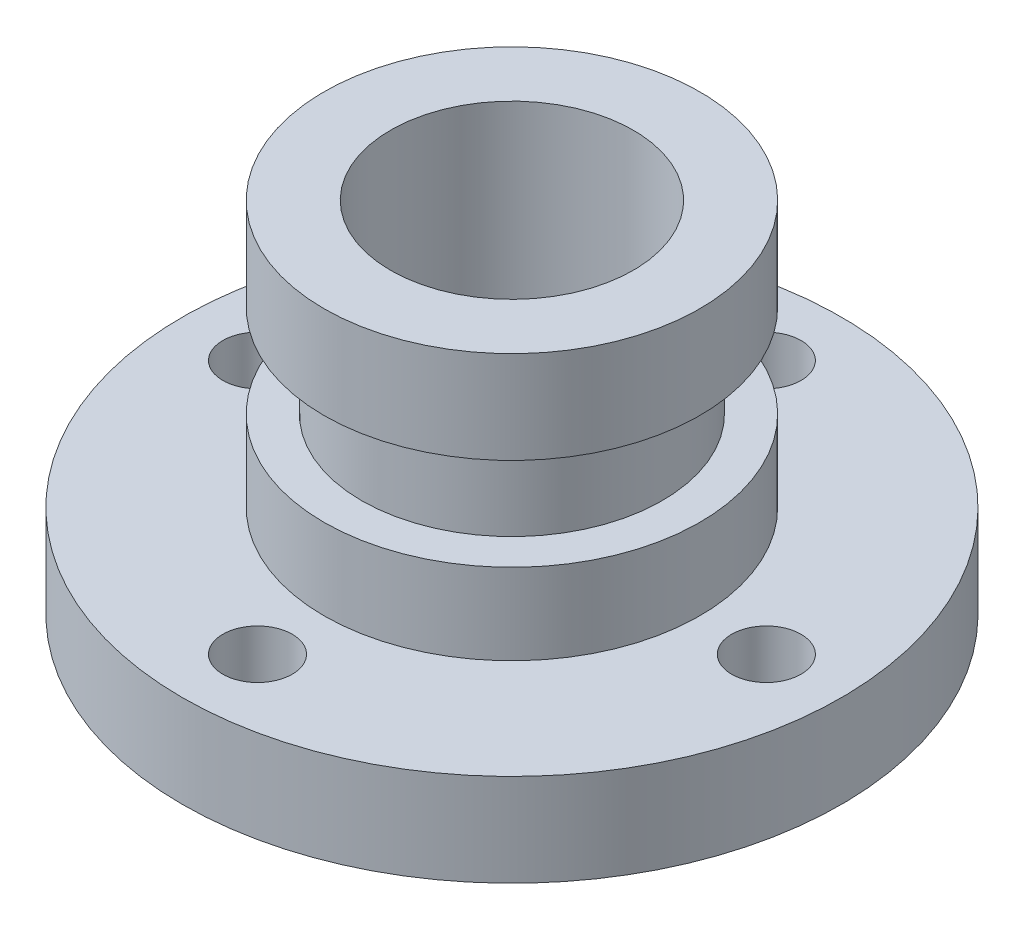
SolidWorks part; units mm, degrees
ref_plane "정면" through (0, 0, 0) normal (0, 0, 1) x (1, 0, 0)
ref_plane "윗면" through (0, 0, 0) normal (0, 1, 0) x (1, 0, 0)
ref_plane "우측면" through (0, 0, 0) normal (1, 0, 0) x (0, 0, -1)
sketch "스케치2" plane through (0, 0, 0) normal (0, 0, 1) x (1, 0, 0)
  line L0 (0, 81.32) -> (0, -101.1226) construction
  line L1 (0, 0) -> (57, 0)
  line L2 (57, 0) -> (57, 16)
  line L3 (57, 16) -> (32.5, 16)
  line L4 (32.5, 16) -> (32.5, 30)
  line L5 (32.5, 30) -> (26, 30)
  line L6 (26, 30) -> (26, 46)
  line L7 (26, 46) -> (32.5, 46)
  line L8 (32.5, 46) -> (32.5, 62)
  line L9 (32.5, 62) -> (0, 62)
  line L10 (0, 62) -> (0, 0)
  point P9 (0, 0)
  point P14 (0, -101.1226)
  point P15 (26, 51.6557)
  dimension "D1" = 57
  dimension "D2" = 32.5
  dimension "D3" = 26
  dimension "D4" = 32.5
  dimension "D5" = 16
  dimension "D6" = 62
  dimension "D7" = 16
  dimension "D8" = 16
revolve "회전1" add sketch "스케치2" angle 360 about L0
sketch "스케치5" plane through (0, 0, 0) normal (0, 0, 1) x (1, 0, 0)
  line L0 (0, 0) -> (15, 0)
  line L1 (-57, 0) -> (57, 0) construction
  line L2 (15, 0) -> (15, 21)
  line L3 (15, 21) -> (21, 27)
  line L4 (21, 27) -> (21, 62)
  line L5 (32.5, 62) -> (-32.5, 62) construction
  line L6 (21, 62) -> (0, 62)
  line L7 (0, 62) -> (0, 0)
  point P7 (15, 21.6672)
  dimension "D1" = 15
  dimension "D2" = 27
  dimension "D3" = 35
  dimension "D4" = 6
  dimension "D5" = 6
revolve "컷-회전1" cut sketch "스케치5" angle 360 about L7
sketch "스케치6" plane through (0, 0, 0) normal (0, 1, 0) x (1, 0, 0)
  line L0 (0, 0) -> (0, 83.1401) construction
  circle A0 centre (0, 44) radius 6
  dimension "D1" = 12
  dimension "D2" = 44
extrude "컷-돌출2" cut sketch "스케치6" along normal through all
pattern_circular "원형 패턴1" count 4 over 360 about axis through (0, 0, 0) along (0, 1, 0) of "컷-돌출2"
